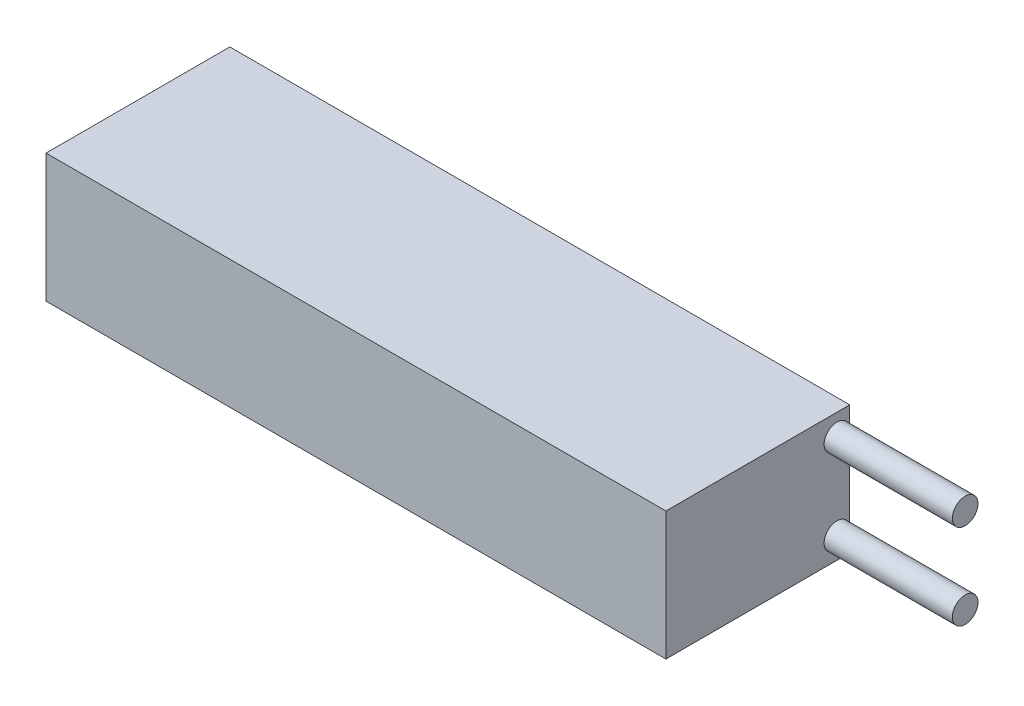
SolidWorks part; units mm, degrees
ref_plane "Front Plane" through (0, 0, 0) normal (0, 0, 1) x (1, 0, 0)
ref_plane "Top Plane" through (0, 0, 0) normal (0, 1, 0) x (1, 0, 0)
ref_plane "Right Plane" through (0, 0, 0) normal (1, 0, 0) x (0, 0, -1)
sketch "Sketch1" plane through (0, 0, 0) normal (0, 1, 0) x (1, 0, 0)
  line L1 (-72.5, -21.5) -> (72.5, -21.5)
  line L2 (-72.5, -21.5) -> (-72.5, 21.5)
  line L3 (-72.5, 21.5) -> (72.5, 21.5)
  line L4 (72.5, -21.5) -> (72.5, 21.5)
  line L5 (-72.5, -21.5) -> (72.5, 21.5) construction
  line L6 (-72.5, 21.5) -> (72.5, -21.5) construction
  point P0 (0, 0)
  dimension "D1" = 43
  dimension "D2" = 145
extrude "Boss-Extrude1" add sketch "Sketch1" along normal blind 30
sketch "Sketch2" plane through (72.5, 0, 0) normal (1, 0, 0) x (0, 0, -1)
  line L0 (21.5, 30) -> (21.5, 0) construction
  line L1 (-21.5, 30) -> (21.5, 30) construction
  line L2 (21.5, 15) -> (-21.5, 15) construction
  line L3 (-21.5, 30) -> (-21.5, 0) construction
  circle A1 centre (18.5, 25) radius 3
  circle A2 centre (18.5, 5) radius 3
  dimension "D3" = 5
  dimension "D1" = 3
extrude "Boss-Extrude2" add sketch "Sketch2" along normal blind 30
